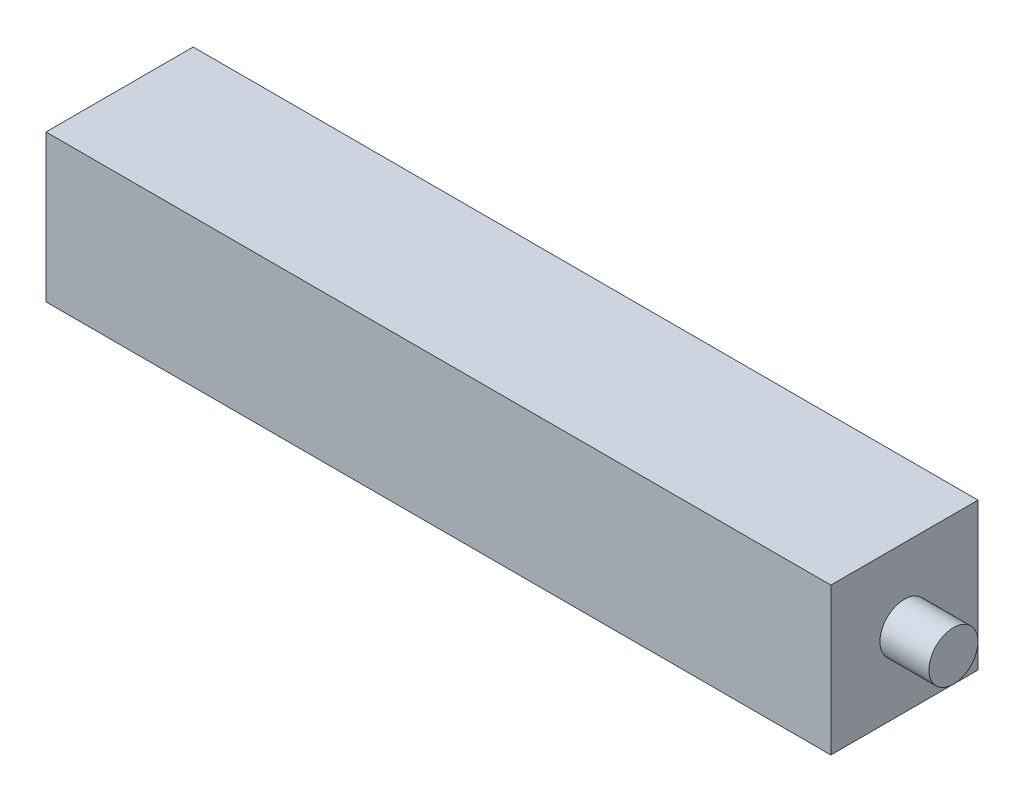
SolidWorks part; units mm, degrees
ref_plane "Alzado" through (0, 0, 0) normal (0, 0, 1) x (1, 0, 0)
ref_plane "Planta" through (0, 0, 0) normal (0, 1, 0) x (1, 0, 0)
ref_plane "Vista lateral" through (0, 0, 0) normal (1, 0, 0) x (0, 0, -1)
sketch "Croquis1" plane through (0, 0, 0) normal (0, 1, 0) x (1, 0, 0)
  line L1 (-101.6, 19.05) -> (101.6, 19.05)
  line L2 (-101.6, 19.05) -> (-101.6, -19.05)
  line L3 (-101.6, -19.05) -> (101.6, -19.05)
  line L4 (101.6, 19.05) -> (101.6, -19.05)
  line L5 (-101.6, 19.05) -> (101.6, -19.05) construction
  line L6 (-101.6, -19.05) -> (101.6, 19.05) construction
  point P0 (0, 0)
  dimension "D1" = 203.2
  dimension "D2" = 38.1
extrude "Saliente-Extruir2" add sketch "Croquis1" along normal blind 38.1
sketch "Croquis2" plane through (101.6, 0, 0) normal (1, 0, 0) x (0, 0, -1)
  line L0 (0, 0) -> (0, 38.1) construction
  line L1 (-19.05, 38.1) -> (19.05, 38.1) construction
  line L2 (-19.05, 19.05) -> (19.05, 19.05) construction
  line L3 (-19.05, 38.1) -> (-19.05, 0) construction
  line L4 (19.05, 38.1) -> (19.05, 0) construction
  circle A1 centre (0, 19.05) radius 6.35
  dimension "D1" = 12.7
extrude "Saliente-Extruir3" add sketch "Croquis2" along normal blind 12.7
sketch "Croquis3" plane through (-101.6, 0, 0) normal (-1, 0, 0) x (0, 0, 1)
  line L0 (0, 0) -> (0, 38.1) construction
  line L1 (-19.05, 38.1) -> (19.05, 38.1) construction
  line L2 (-19.05, 19.05) -> (19.05, 19.05) construction
  line L3 (-19.05, 38.1) -> (-19.05, 0) construction
  line L4 (19.05, 38.1) -> (19.05, 0) construction
  circle A0 centre (0, 19.05) radius 6.35
  dimension "D1" = 12.7
extrude "Saliente-Extruir4" add sketch "Croquis3" along normal blind 12.7
ref_plane "Plano1" through (0, 0, 0) normal (-1, 0, 0) x (0, 0, 1)
